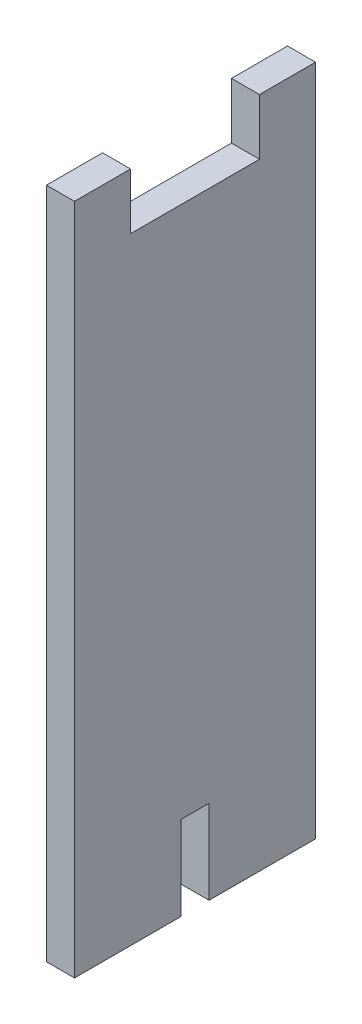
SolidWorks part; units mm, degrees
ref_plane "Front Plane" through (0, 0, 0) normal (0, 0, 1) x (1, 0, 0)
ref_plane "Top Plane" through (0, 0, 0) normal (0, 1, 0) x (1, 0, 0)
ref_plane "Right Plane" through (0, 0, 0) normal (1, 0, 0) x (0, 0, -1)
sketch "Sketch1" plane through (0, 0, 0) normal (1, 0, 0) x (0, 0, -1)
  line L0 (-33, 120) -> (-33, 111.226)
  line L1 (0, 0) -> (-19, 0)
  line L2 (0, 0) -> (0, 120)
  line L3 (0, 120) -> (-10, 120)
  line L4 (-43, 0) -> (-43, 120)
  line L6 (-10, 111.226) -> (-10, 120)
  line L7 (-33, 120) -> (-43, 120)
  line L8 (-24, 0) -> (-24, 15)
  line L9 (-24, 15) -> (-19, 15)
  line L10 (-19, 15) -> (-19, 0)
  line L11 (-24, 0) -> (-43, 0)
  line L12 (-33, 111.226) -> (-33, 110)
  line L13 (-33, 110) -> (-10, 110)
  line L14 (-10, 110) -> (-10, 111.226)
  point P7 (-33, 115.613)
  dimension "D1" = 43
  dimension "D2" = 120
  dimension "D3" = 10
  dimension "D4" = 10
  dimension "D5" = 5
  dimension "D6" = 15
  dimension "D7" = 19
  dimension "D8" = 10
extrude "Boss-Extrude1" add sketch "Sketch1" along normal blind 5
